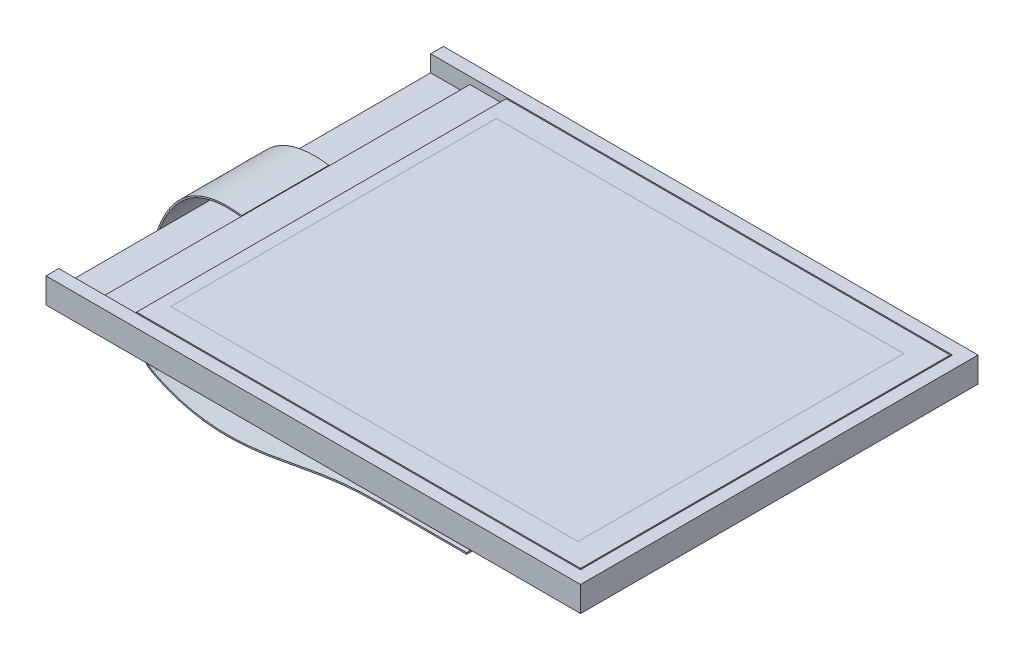
SolidWorks part; units mm, degrees
ref_plane "Front Plane" through (0, 0, 0) normal (0, 0, 1) x (1, 0, 0)
ref_plane "Top Plane" through (0, 0, 0) normal (0, 1, 0) x (1, 0, 0)
ref_plane "Right Plane" through (0, 0, 0) normal (1, 0, 0) x (0, 0, -1)
sketch "Sketch1" plane through (0, 0, 0) normal (0, 1, 0) x (1, 0, 0)
  line L1 (-22.9, 17) -> (22.9, 17)
  line L2 (-22.9, 17) -> (-22.9, -17)
  line L3 (-22.9, -17) -> (22.9, -17)
  line L4 (22.9, 17) -> (22.9, -17)
  dimension "D1" = 34
  dimension "D2" = 45.8
  dimension "D3" = 22.9
  dimension "D4" = 17
extrude "Boss-Extrude1" add sketch "Sketch1" along normal blind 2.17
sketch "Sketch2" plane through (0, 2.17, 0) normal (0, 1, 0) x (1, 0, 0)
  line L6 (-22.9, 16) -> (-22.9, -16)
  line L9 (-22.9, -16) -> (21.9, -16)
  line L10 (21.9, -16) -> (21.9, 16)
  line L11 (21.9, 16) -> (-22.9, 16)
  line L12 (-22.9, -16) -> (21.9, -16)
  line L13 (21.9, -16) -> (21.9, 16)
  line L14 (21.9, 16) -> (-22.9, 16)
  dimension "D1" = 1
extrude "Cut-Extrude1" cut sketch "Sketch2" against normal offset from surface (1.42 mm away) 0.75 up to face at (0, 0, 0)
sketch "Sketch3" plane through (0, 0.75, 0) normal (0, 1, 0) x (1, 0, 0)
  line L6 (-19.52, 15.9) -> (-19.52, -15.9)
  line L7 (21.9, -16) -> (21.9, 16) construction
  line L9 (-22.9, -15.9) -> (21.8, -15.9)
  line L10 (21.8, -15.9) -> (21.8, 15.9)
  line L11 (21.8, 15.9) -> (-22.9, 15.9)
  line L12 (-19.52, -15.9) -> (21.8, -15.9)
  line L13 (21.8, -15.9) -> (21.8, 15.9)
  line L14 (21.8, 15.9) -> (-19.52, 15.9)
  dimension "D2" = 41.42
  dimension "D1" = 0.1
extrude "Boss-Extrude3" add sketch "Sketch3" along normal up to surface (1.42 mm away) separate body up to face at (-0.25, 2.17, 0)
sketch "Sketch9" plane through (0, 2.17, 0) normal (0, 1, 0) x (1, 0, 0)
  line L1 (-15.35, 14.015) -> (19.69, 14.015)
  line L2 (-15.35, 14.015) -> (-15.35, -14.015)
  line L3 (-15.35, -14.015) -> (19.69, -14.015)
  line L4 (19.69, 14.015) -> (19.69, -14.015)
  line L5 (21.9, 16) -> (21.9, -16) construction
  dimension "D1" = 2.21
  dimension "D2" = 14.015
  dimension "D3" = 28.03
  dimension "D4" = 35.04
split line "Split Line3"
sketch "Sketch10" plane through (0, 2.17, 0) normal (0, 1, 0) x (1, 0, 0)
  line L0 (-19.52, -15.9) -> (21.8, -15.9) construction
  line L1 (-19.52, 15.9) -> (-16.4, 15.9)
  line L2 (-19.52, 15.9) -> (-19.52, -15.9)
  line L3 (-19.52, -15.9) -> (-16.4, -15.9)
  line L4 (-16.4, 15.9) -> (-16.4, -15.9)
  line L8 (22.9, -17) -> (22.9, 17) construction
  dimension "D1" = 39.3
extrude "Cut-Extrude2" cut sketch "Sketch10" against normal blind 0.5
sketch "Sketch5" plane through (0, 0, 0) normal (0, 0, 1) x (1, 0, 0)
  line L0 (-0.15, -13.77) -> (-27.15, -13.77) construction
  line L2 (-0.15, -13.77) -> (-7.65, -13.77)
  line L3 (-22.9, 0) -> (22.9, 0) construction
  line L5 (-0.15, -15.02) -> (-0.15, -15.52) construction
  spline S0 degree 3 poles (-27.15, -13.77) (-28.8019, -12.9129) (-28.4113, -9.6974) (-26.3111, -0.7256) (-23.4704, 2.2321) (-19.52, 1.67) knots 0 0 0 0 0.519172 0.661297 1 1 1 1
  spline S1 degree 3 poles (-27.15, -13.77) (-23.1887, -15.8255) (-16.4527, -15.0329) (-11.1913, -13.77) (-7.65, -13.77) knots 0 0 0 0 0.574024 1 1 1 1
  dimension "D1" = 13.77
  dimension "D2" = 7.5
  dimension "D3" = 27
ref_plane "Plane1" through (-0.15, 0, 0) normal (1, 0, 0) x (0, 0, -1)
sketch "Sketch6" plane through (-0.15, 0, 0) normal (1, 0, 0) x (0, 0, -1)
  line L0 (0, 1.7621) -> (0, -13.77) construction
  line L1 (-3.75, -13.7075) -> (3.75, -13.7075)
  line L2 (-3.75, -13.7075) -> (-3.75, -13.8325)
  line L3 (-3.75, -13.8325) -> (3.75, -13.8325)
  line L4 (3.75, -13.7075) -> (3.75, -13.8325)
  line L5 (-3.75, -13.7075) -> (3.75, -13.8325) construction
  line L6 (-3.75, -13.8325) -> (3.75, -13.7075) construction
  point P0 (0, -13.77)
  dimension "D1" = 7.5
  dimension "D2" = 0.125
sweep "Sweep1" add profiles "Sketch6" path "Sketch5"
sketch "Sketch7" plane through (0, -13.8325, 0) normal (0, -1, 0) x (1, 0, 0)
  line L1 (-0.15, 3.75) -> (-5.15, 3.75)
  line L2 (-0.15, 3.75) -> (-0.15, -3.75)
  line L3 (-0.15, -3.75) -> (-5.15, -3.75)
  line L4 (-5.15, 3.75) -> (-5.15, -3.75)
  line L7 (-0.15, -3.75) -> (-7.65, -3.75) construction
  dimension "D1" = 5
split line "Split Line1"
sketch "Sketch8" plane through (0, -13.7075, 0) normal (0, 1, 0) x (1, 0, 0)
  line L1 (-0.15, 3.425) -> (-5.15, 3.425)
  line L2 (-0.15, 3.425) -> (-0.15, 3.075)
  line L3 (-0.15, 3.075) -> (-5.15, 3.075)
  line L4 (-5.15, 3.425) -> (-5.15, 3.075)
  line L5 (-0.15, 2.925) -> (-0.15, 2.575)
  line L6 (-0.15, 2.925) -> (-5.15, 2.925)
  line L7 (-5.15, 2.925) -> (-5.15, 2.575)
  line L8 (-0.15, 2.575) -> (-5.15, 2.575)
  line L9 (-0.15, 2.425) -> (-0.15, 2.075)
  line L10 (-0.15, 2.425) -> (-5.15, 2.425)
  line L11 (-5.15, 2.425) -> (-5.15, 2.075)
  line L12 (-0.15, 2.075) -> (-5.15, 2.075)
  line L13 (-0.15, 1.925) -> (-0.15, 1.575)
  line L14 (-0.15, 1.925) -> (-5.15, 1.925)
  line L15 (-5.15, 1.925) -> (-5.15, 1.575)
  line L16 (-0.15, 1.575) -> (-5.15, 1.575)
  line L17 (-0.15, 1.425) -> (-0.15, 1.075)
  line L18 (-0.15, 1.425) -> (-5.15, 1.425)
  line L19 (-5.15, 1.425) -> (-5.15, 1.075)
  line L20 (-0.15, 1.075) -> (-5.15, 1.075)
  line L21 (-0.15, 0.925) -> (-0.15, 0.575)
  line L22 (-0.15, 0.925) -> (-5.15, 0.925)
  line L23 (-5.15, 0.925) -> (-5.15, 0.575)
  line L24 (-0.15, 0.575) -> (-5.15, 0.575)
  line L25 (-0.15, 0.425) -> (-0.15, 0.075)
  line L26 (-0.15, 0.425) -> (-5.15, 0.425)
  line L27 (-5.15, 0.425) -> (-5.15, 0.075)
  line L28 (-0.15, 0.075) -> (-5.15, 0.075)
  line L29 (-0.15, -0.075) -> (-0.15, -0.425)
  line L30 (-0.15, -0.075) -> (-5.15, -0.075)
  line L31 (-5.15, -0.075) -> (-5.15, -0.425)
  line L32 (-0.15, -0.425) -> (-5.15, -0.425)
  line L33 (-0.15, -0.575) -> (-0.15, -0.925)
  line L34 (-0.15, -0.575) -> (-5.15, -0.575)
  line L35 (-5.15, -0.575) -> (-5.15, -0.925)
  line L36 (-0.15, -0.925) -> (-5.15, -0.925)
  line L37 (-0.15, -1.075) -> (-0.15, -1.425)
  line L38 (-0.15, -1.075) -> (-5.15, -1.075)
  line L39 (-5.15, -1.075) -> (-5.15, -1.425)
  line L40 (-0.15, -1.425) -> (-5.15, -1.425)
  line L41 (-0.15, -1.575) -> (-0.15, -1.925)
  line L42 (-0.15, -1.575) -> (-5.15, -1.575)
  line L43 (-5.15, -1.575) -> (-5.15, -1.925)
  line L44 (-0.15, -1.925) -> (-5.15, -1.925)
  line L45 (-0.15, -2.075) -> (-0.15, -2.425)
  line L46 (-0.15, -2.075) -> (-5.15, -2.075)
  line L47 (-5.15, -2.075) -> (-5.15, -2.425)
  line L48 (-0.15, -2.425) -> (-5.15, -2.425)
  line L49 (-0.15, -2.575) -> (-0.15, -2.925)
  line L50 (-0.15, -2.575) -> (-5.15, -2.575)
  line L51 (-5.15, -2.575) -> (-5.15, -2.925)
  line L52 (-0.15, -2.925) -> (-5.15, -2.925)
  line L53 (-0.15, -3.075) -> (-0.15, -3.425)
  line L54 (-0.15, -3.075) -> (-5.15, -3.075)
  line L55 (-5.15, -3.075) -> (-5.15, -3.425)
  line L56 (-0.15, -3.425) -> (-5.15, -3.425)
  line L62 (-0.15, 3.75) -> (-0.15, -3.75) construction
  line L63 (-0.15, 3.75) -> (-7.65, 3.75) construction
  dimension "D1" = 5
  dimension "D2" = 0.35
  dimension "D4" = 0.325
  dimension "D3" = 14
split line "Split Line2"
other "Move Face1" face at (-22.9, 1.2725, 0) face at (0, 1.085, -17) face at (22.9, 1.085, 0) face at (0, 1.085, 17) parameters "D1"=0.1
